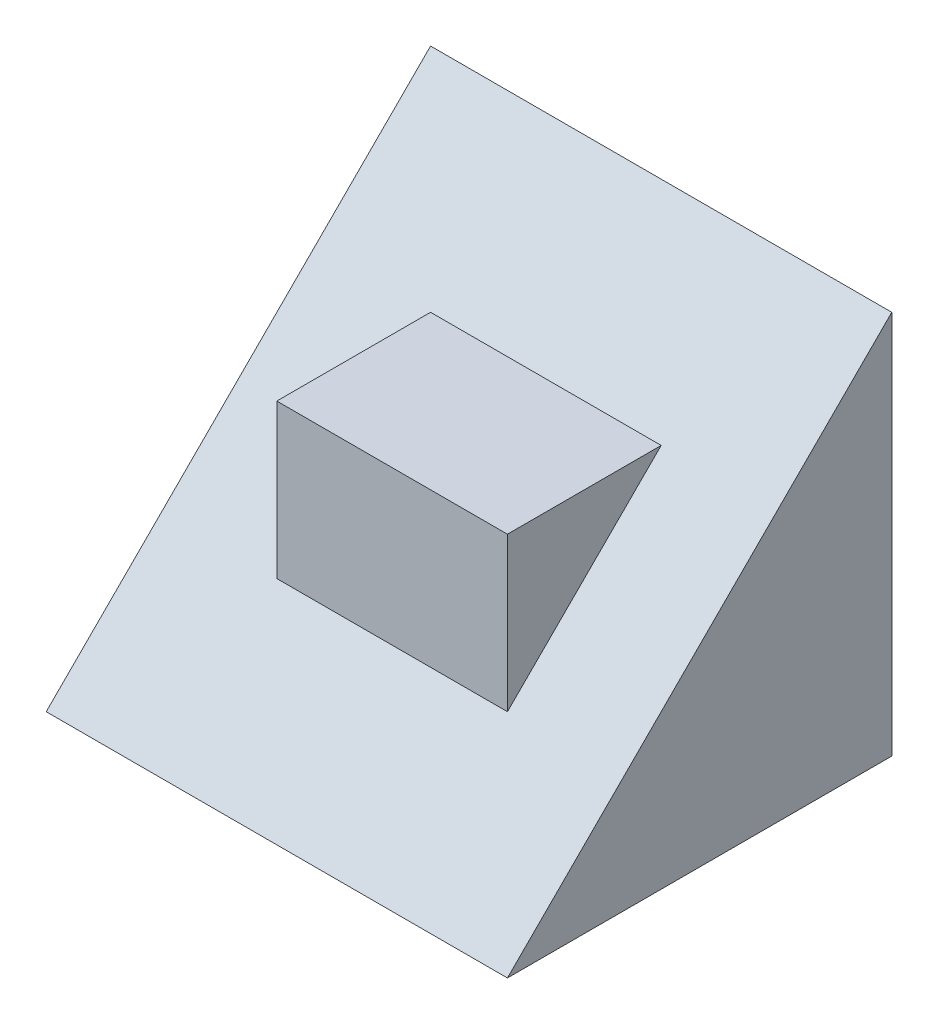
SolidWorks part; units mm, degrees
ref_plane "Front Plane" through (0, 0, 0) normal (0, 0, 1) x (1, 0, 0)
ref_plane "Top Plane" through (0, 0, 0) normal (0, 1, 0) x (1, 0, 0)
ref_plane "Right Plane" through (0, 0, 0) normal (1, 0, 0) x (0, 0, -1)
sketch "Sketch1" plane through (0, 0, 0) normal (1, 0, 0) x (0, 0, -1)
  line L0 (0, 0) -> (0, 50)
  line L1 (0, 50) -> (-50, 0)
  line L2 (-50, 0) -> (0, 0)
  dimension "D1" = 50
extrude "Boss-Extrude1" add sketch "Sketch1" along normal mid plane 60
sketch "Sketch2" plane through (0, 0, 0) normal (1, 0, 0) x (0, 0, -1)
  line L1 (0, 0) -> (-35, 0)
  line L2 (0, 0) -> (0, 35)
  line L3 (0, 35) -> (-35, 35)
  line L4 (-35, 0) -> (-35, 35)
  dimension "D1" = 35
extrude "Boss-Extrude2" add sketch "Sketch2" along normal mid plane 30
